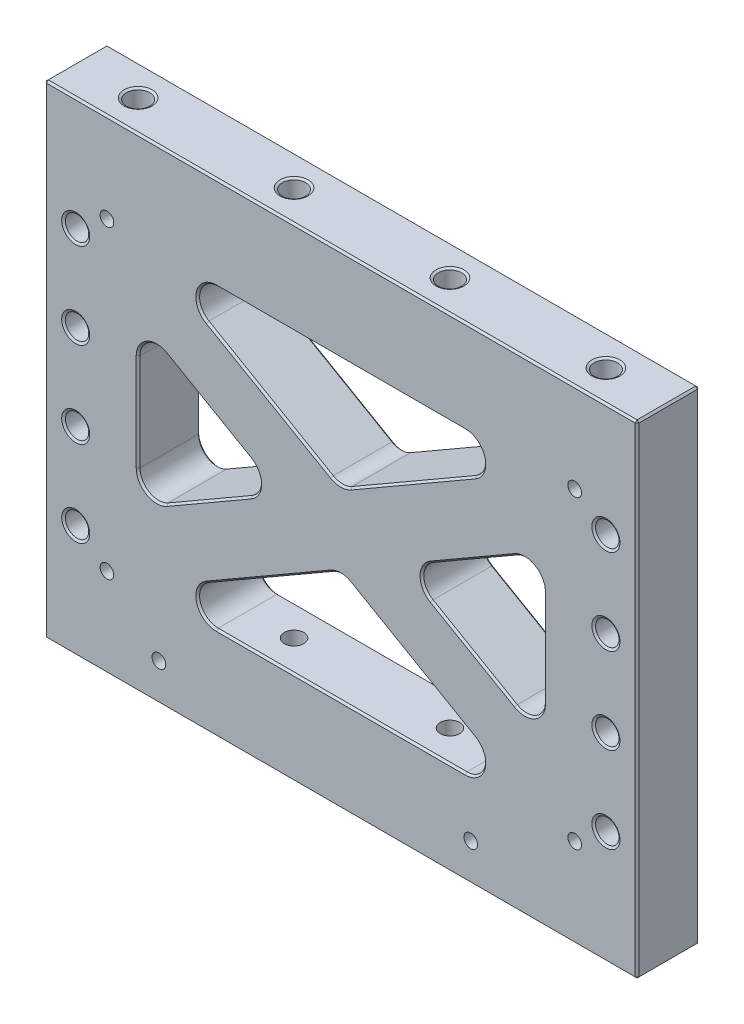
SolidWorks part; units mm, degrees
material "6061-T6 Al"
ref_plane "Front" through (0, 0, 0) normal (0, 0, 1) x (1, 0, 0)
ref_plane "Top" through (0, 0, 0) normal (0, 1, 0) x (1, 0, 0)
ref_plane "Right" through (0, 0, 0) normal (1, 0, 0) x (0, 0, -1)
sketch "Sketch1" plane through (0, 0, 0) normal (0, 0, 1) x (1, 0, 0)
  line L1 (-120.65, 0) -> (120.65, 0)
  line L2 (-120.65, 0) -> (-120.65, 196.85)
  line L3 (-120.65, 196.85) -> (120.65, 196.85)
  line L4 (120.65, 0) -> (120.65, 196.85)
  dimension "D1" = 241.3
  dimension "D2" = 196.85
extrude "Extrude1" add sketch "Sketch1" along normal blind 25.4
sketch "Sketch8" plane through (0, 0, 25.4) normal (0, 0, 1) x (1, 0, 0)
  line L0 (0, 158.75) -> (0, 196.85) construction
  line L1 (-82.55, 158.75) -> (82.55, 158.75)
  line L2 (-82.55, 158.75) -> (-82.55, 38.1)
  line L3 (-82.55, 38.1) -> (82.55, 38.1)
  line L4 (82.55, 158.75) -> (82.55, 38.1)
  line L5 (120.65, 196.85) -> (-120.65, 196.85) construction
  line L6 (0, 0) -> (0, 38.1) construction
  line L7 (-120.65, 0) -> (120.65, 0) construction
  line L8 (120.65, 0) -> (120.65, 196.85) construction
  point P4 (0, 38.1)
  dimension "D1" = 38.1
  dimension "D2" = 38.1
extrude "Extrude2" cut sketch "Sketch8" against normal through all
sketch "Sketch9" plane through (0, 0, 25.4) normal (0, 0, 1) x (1, 0, 0)
  line L0 (-82.55, 146.0853) -> (82.55, 50.7647) construction
  line L1 (-82.55, 38.1) -> (82.55, 38.1) construction
  line L2 (0, 98.425) -> (120.65, 98.425) construction
  line L3 (120.65, 0) -> (120.65, 196.85) construction
  line L4 (82.55, 38.1) -> (82.55, 158.75) construction
  line L5 (-82.55, 158.75) -> (-82.55, 131.4206)
  line L6 (-82.55, 158.75) -> (-82.55, 38.1) construction
  line L7 (-82.55, 131.4206) -> (79.086, 38.1)
  line L8 (79.086, 38.1) -> (82.55, 38.1)
  line L9 (82.55, 38.1) -> (82.55, 65.4294)
  line L10 (82.55, 65.4294) -> (-79.086, 158.75)
  line L11 (82.55, 158.75) -> (-82.55, 158.75) construction
  line L12 (-79.086, 158.75) -> (-82.55, 158.75)
  line L13 (-6.35, 87.4265) -> (0, 98.425) construction
  line L14 (0, 98.425) -> (6.35, 109.4235) construction
  dimension "D1" = 30
  dimension "D2" = 25.4
extrude "Extrude3" add sketch "Sketch9" against normal up to surface (25.4 mm away) up to face at (0, 98.425, 0)
mirror "Mirror1" about plane through (0, 0, 0) normal (1, 0, 0) of "Extrude3"
fillet "Fillet1" radius 7.62 12 edges at (79.086, 38.1, 12.7) (-79.086, 38.1, 12.7) (0, 83.7603, 12.7) (79.086, 158.75, 12.7) (0, 113.0897, 12.7) (-82.55, 65.4294, 12.7) (-82.55, 131.4206, 12.7) (-25.4, 98.425, 12.7) (82.55, 131.4206, 12.7) (82.55, 65.4294, 12.7) (25.4, 98.425, 12.7) (-79.086, 158.75, 12.7)
chamfer "Chamfer1" distance 0.762 angle 45 48 edges at (29.1339, 66.9399, 25.4) (29.1339, 66.9399, 0) (58.0081, 43.7478, 25.4) (0, 82.5815, 25.4) (0, 38.1, 25.4) (-29.1339, 66.9399, 25.4) (-29.1339, 66.9399, 0) (-58.0081, 43.7478, 25.4) (0, 82.5815, 0) (58.0081, 43.7478, 0) (0, 38.1, 0) (-58.0081, 43.7478, 0) (53.975, 114.9228, 0) (53.975, 114.9228, 25.4) (78.74, 124.8215, 25.4) (33.02, 98.425, 25.4) (82.55, 98.425, 25.4) (53.975, 81.9272, 25.4) (53.975, 81.9272, 0) (78.74, 72.0285, 25.4) (33.02, 98.425, 0) (78.74, 124.8215, 0) (82.55, 98.425, 0) (78.74, 72.0285, 0) (0, 158.75, 0) (-58.0081, 153.1022, 0) (58.0081, 153.1022, 0) (-29.1339, 129.9101, 25.4) (-29.1339, 129.9101, 0) (29.1339, 129.9101, 25.4) (29.1339, 129.9101, 0) (0, 114.2685, 0) (0, 158.75, 25.4) (58.0081, 153.1022, 25.4) (-58.0081, 153.1022, 25.4) (0, 114.2685, 25.4) (-53.975, 114.9228, 25.4) (-53.975, 114.9228, 0) (-33.02, 98.425, 25.4) (-78.74, 124.8215, 25.4) (-53.975, 81.9272, 0) (-53.975, 81.9272, 25.4) (-82.55, 98.425, 25.4) (-78.74, 72.0285, 25.4) (-78.74, 124.8215, 0) (-33.02, 98.425, 0) (-82.55, 98.425, 0) (-78.74, 72.0285, 0)
chamfer "Chamfer2" distance 0.762 angle 45 12 edges at (-120.65, 98.425, 25.4) (-120.65, 98.425, 0) (-120.65, 0, 12.7) (0, 0, 25.4) (0, 0, 0) (120.65, 0, 12.7) (120.65, 98.425, 25.4) (120.65, 98.425, 0) (120.65, 196.85, 12.7) (0, 196.85, 25.4) (-120.65, 196.85, 12.7) (0, 196.85, 0)
hole_wizard "3/8-16 Tapped Hole1" positions "Sketch5" profile "Sketch4" tap size "3/8-16" standard "Ansi Inch"
sketch "Sketch5" plane through (0, 196.85, 0) normal (0, 1, 0) x (-1, 0, 0)
  line L2 (-95.25, 12.7) -> (-31.75, 12.7) construction
  line L3 (-31.75, 12.7) -> (31.75, 12.7) construction
  line L4 (31.75, 12.7) -> (95.25, 12.7) construction
  line L7 (120.65, 25.4) -> (120.65, 0) construction
  point P1 (31.75, 12.7)
  point P3 (-31.75, 12.7)
  point P42 (0, 12.7)
  point P46 (120.65, 12.7)
  dimension "D1" = 63.5
sketch "Sketch4" plane through (-31.75, 196.85, 12.7) normal (1, 0, 0) x (0, 0, 1)
  line L0 (0, 0) -> (0, 40.4847)
  line L1 (0, 40.4847) -> (3.9687, 38.1)
  line L2 (3.9687, 38.1) -> (3.9687, 25.4)
  line L3 (3.9687, 25.4) -> (4.7625, 25.4)
  line L5 (4.7625, 25.4) -> (4.7625, 0.5499)
  line L6 (4.7625, 0.5499) -> (5.715, 0)
  line L7 (5.715, 0) -> (0, 0)
  line L8 (-4.7625, 0.5499) -> (-5.715, 0) construction
  line L10 (0, 40.4847) -> (-3.9688, 38.1) construction
  line L11 (0, -6.35) -> (0, 107.95) construction
  dimension "Tap Drill Dia." = 7.9375
  dimension "Tap Drill Depth" = 38.1
  dimension "Thread Major Dia." = 9.525
  dimension "Thread Depth" = 25.4
  dimension "Near C'Sink Dia." = 11.43
  dimension "Near C'Sink Angle" = 120
  dimension "Drill Angle" = 118
hole_wizard "3/8-16 Tapped Hole2" positions "Sketch29" profile "Sketch28" tap size "3/8-16" standard "Ansi Inch"
sketch "Sketch29" plane through (0, 0, 0) normal (0, -1, 0) x (1, 0, 0)
  point P1 (-31.75, 12.7)
  point P4 (31.75, 12.7)
sketch "Sketch28" plane through (-31.75, 0, 12.7) normal (1, 0, 0) x (0, 0, -1)
  line L0 (0, 0) -> (0, 40.4847)
  line L1 (0, 40.4847) -> (3.9687, 38.1)
  line L2 (3.9687, 38.1) -> (3.9687, 25.4)
  line L3 (3.9687, 25.4) -> (4.7625, 25.4)
  line L5 (4.7625, 25.4) -> (4.7625, 0.5499)
  line L6 (4.7625, 0.5499) -> (5.715, 0)
  line L7 (5.715, 0) -> (0, 0)
  line L8 (-4.7625, 0.5499) -> (-5.715, 0) construction
  line L10 (0, 40.4847) -> (-3.9688, 38.1) construction
  line L11 (0, -6.35) -> (0, 107.95) construction
  dimension "Tap Drill Dia." = 7.9375
  dimension "Tap Drill Depth" = 38.1
  dimension "Thread Major Dia." = 9.525
  dimension "Thread Depth" = 25.4
  dimension "Near C'Sink Dia." = 11.43
  dimension "Near C'Sink Angle" = 120
  dimension "Drill Angle" = 118
hole_wizard "3/8-16 Tapped Hole3" positions "Sketch35" profile "Sketch34" tap size "3/8-16" standard "Ansi Inch"
sketch "Sketch35" plane through (0, 196.85, 0) normal (0, 1, 0) x (-1, 0, 0)
  line L0 (-95.25, 12.7) -> (-31.75, 12.7) construction
  line L3 (31.75, 12.7) -> (95.25, 12.7) construction
  line L6 (-31.75, 12.7) -> (31.75, 12.7) construction
  point P0 (95.25, 12.7)
  point P1 (-95.25, 12.7)
sketch "Sketch34" plane through (-95.25, 196.85, 12.7) normal (1, 0, 0) x (0, 0, 1)
  line L0 (0, 0) -> (0, 40.4847)
  line L1 (0, 40.4847) -> (3.9687, 38.1)
  line L2 (3.9687, 38.1) -> (3.9687, 25.4)
  line L3 (3.9687, 25.4) -> (4.7625, 25.4)
  line L5 (4.7625, 25.4) -> (4.7625, 0.5499)
  line L6 (4.7625, 0.5499) -> (5.715, 0)
  line L7 (5.715, 0) -> (0, 0)
  line L8 (-4.7625, 0.5499) -> (-5.715, 0) construction
  line L10 (0, 40.4847) -> (-3.9688, 38.1) construction
  line L11 (0, -6.35) -> (0, 107.95) construction
  dimension "Tap Drill Dia." = 7.9375
  dimension "Tap Drill Depth" = 38.1
  dimension "Thread Major Dia." = 9.525
  dimension "Thread Depth" = 25.4
  dimension "Near C'Sink Dia." = 11.43
  dimension "Near C'Sink Angle" = 120
  dimension "Drill Angle" = 118
hole_wizard "3/8-16 Tapped Hole4" positions "Sketch37" profile "Sketch36" tap size "3/8-16" standard "Ansi Inch"
sketch "Sketch37" plane through (0, 0, 0) normal (0, -1, 0) x (1, 0, 0)
  point P0 (95.25, 12.7)
  point P4 (-95.25, 12.7)
sketch "Sketch36" plane through (95.25, 0, 12.7) normal (1, 0, 0) x (0, 0, -1)
  line L0 (0, 0) -> (0, 40.4847)
  line L1 (0, 40.4847) -> (3.9687, 38.1)
  line L2 (3.9687, 38.1) -> (3.9687, 25.4)
  line L3 (3.9687, 25.4) -> (4.7625, 25.4)
  line L5 (4.7625, 25.4) -> (4.7625, 0.5499)
  line L6 (4.7625, 0.5499) -> (5.715, 0)
  line L7 (5.715, 0) -> (0, 0)
  line L8 (-4.7625, 0.5499) -> (-5.715, 0) construction
  line L10 (0, 40.4847) -> (-3.9688, 38.1) construction
  line L11 (0, -6.35) -> (0, 107.95) construction
  dimension "Tap Drill Dia." = 7.9375
  dimension "Tap Drill Depth" = 38.1
  dimension "Thread Major Dia." = 9.525
  dimension "Thread Depth" = 25.4
  dimension "Near C'Sink Dia." = 11.43
  dimension "Near C'Sink Angle" = 120
  dimension "Drill Angle" = 118
hole_wizard "7/32 (0.21875) Vent Hole1" positions "Sketch3" profile "Sketch2" hole size "7/32" standard "Ansi Inch" end condition through all
sketch "Sketch3" plane through (0, 0, 25.4) normal (0, 0, 1) x (1, 0, 0)
  line L15 (31.75, 160.528) -> (95.25, 160.528) construction
  line L16 (-31.75, 160.528) -> (31.75, 160.528) construction
  line L17 (-95.25, 160.528) -> (-31.75, 160.528) construction
  line L26 (0, 160.528) -> (0, 196.85) construction
  line L27 (120.65, 196.85) -> (-120.65, 196.85) construction
  line L29 (-95.25, 36.322) -> (-95.25, 0) construction
  line L30 (119.888, 0) -> (-119.888, 0) construction
  line L32 (-119.888, 196.85) -> (119.888, 196.85) construction
  point P69 (-95.25, 160.528)
  point P75 (95.25, 160.528)
  point P95 (-95.25, 36.322)
  point P101 (95.25, 36.322)
  dimension "D1" = 36.322
  dimension "D2" = 63.5
sketch "Sketch2" plane through (-95.25, 160.528, 25.4) normal (1, 0, 0) x (0, -1, 0)
  line L0 (0, 0) -> (0, 25.4)
  line L1 (0, 25.4) -> (2.7781, 25.4)
  line L2 (2.7781, 25.4) -> (2.7781, 0)
  line L5 (2.7781, 0) -> (0, 0)
  line L11 (0, -6.35) -> (0, 107.95) construction
  dimension "Thru Hole Dia." = 5.5562
  dimension "Thru Hole Depth" = 25.4
hole_wizard "3/8-16 Tapped Hole5" positions "Sketch33" profile "Sketch32" tap size "3/8-16" standard "Ansi Inch" end condition through all
sketch "Sketch33" plane through (32.6062, 166.8277, 0) normal (0, 0, -1) x (-1, 0, 0)
  line L0 (-75.3438, -16.0152) -> (-75.3438, -50.9402) construction
  line L1 (-75.3438, -50.9402) -> (-75.3438, -85.8652) construction
  line L2 (-75.3438, -85.8652) -> (-75.3438, -120.7902) construction
  line L9 (140.5562, -16.0152) -> (153.2562, -16.0152) construction
  line L10 (153.2562, 29.2603) -> (153.2562, -166.0657) construction
  line L13 (-75.3438, -68.4027) -> (-88.0438, -68.4027) construction
  line L14 (-88.0438, -166.0657) -> (-88.0438, 29.2603) construction
  point P0 (-75.3438, -16.0152)
  point P3 (-75.3438, -50.9402)
  point P5 (-75.3438, -85.8652)
  point P7 (-75.3438, -120.7902)
  point P9 (140.5562, -120.7902)
  point P11 (140.5562, -85.8652)
  point P13 (140.5562, -50.9402)
  point P15 (140.5562, -16.0152)
  dimension "D1" = 34.925
  dimension "D2" = 12.7
sketch "Sketch32" plane through (107.95, 150.8125, 0) normal (1, 0, 0) x (0, 1, 0)
  line L0 (0, 0) -> (0, 25.4)
  line L1 (0, 25.4) -> (5.715, 25.4)
  line L2 (4.7625, 24.8501) -> (4.7625, 0.5499)
  line L3 (4.7625, 0.5499) -> (5.715, 0)
  line L5 (5.715, 0) -> (0, 0)
  line L6 (-4.7625, 0.5499) -> (-5.715, 0) construction
  line L7 (5.715, 25.4) -> (4.7625, 24.8501)
  line L8 (-5.715, 25.4) -> (-4.7625, 24.8501) construction
  line L11 (0, -6.35) -> (0, 107.95) construction
  dimension "Thread Major Dia." = 9.525
  dimension "Thru Tap Drill Depth" = 25.4
  dimension "Near C'Sink Dia." = 11.43
  dimension "Near C'Sink Angle" = 120
  dimension "Far C'Sink Dia." = 11.43
  dimension "Far C'Sink Angle" = 120
sketch "Sketch38" [suppressed] plane through (0, 0, 0) normal (0, -1, 0) x (1, 0, 0)
  line L4 (-120.65, 0) -> (120.65, 0)
  line L5 (120.65, 0) -> (120.65, 25.4)
  line L6 (120.65, 25.4) -> (-120.65, 25.4)
  line L7 (-120.65, 25.4) -> (-120.65, 0)
  line L8 (-120.65, 0) -> (120.65, 0)
  line L9 (120.65, 0) -> (120.65, 25.4)
  line L10 (120.65, 25.4) -> (-120.65, 25.4)
  line L11 (-120.65, 25.4) -> (-120.65, 0)
  dimension "D1" = 0
extrude "Extrude4" [suppressed] cut sketch "Sketch38" against normal blind 0.0254
sketch "Sketch39" [suppressed] plane through (0, 196.85, 0) normal (0, 1, 0) x (1, 0, 0)
  line L4 (120.65, 0) -> (-120.65, 0)
  line L5 (-120.65, 0) -> (-120.65, -25.4)
  line L6 (-120.65, -25.4) -> (120.65, -25.4)
  line L7 (120.65, -25.4) -> (120.65, 0)
  line L8 (120.65, 0) -> (-120.65, 0)
  line L9 (-120.65, 0) -> (-120.65, -25.4)
  line L10 (-120.65, -25.4) -> (120.65, -25.4)
  line L11 (120.65, -25.4) -> (120.65, 0)
  dimension "D1" = 0
extrude "Extrude5" [suppressed] cut sketch "Sketch39" against normal blind 0.0254
sketch "Sketch40" [suppressed] plane through (0, 0.0254, 0) normal (0, -1, 0) x (1, 0, 0)
  line L0 (120.65, 25.4) -> (-120.65, 25.4) construction
  line L1 (-44.45, 25.4) -> (-19.05, 25.4)
  line L2 (-44.45, 25.4) -> (-44.45, 0)
  line L3 (-44.45, 0) -> (-19.05, 0)
  line L4 (-19.05, 25.4) -> (-19.05, 0)
  line L5 (-120.65, 0) -> (120.65, 0) construction
  line L6 (-82.55, 12.7) -> (-44.45, 12.7) construction
  line L7 (-107.95, 25.4) -> (-82.55, 25.4)
  line L8 (-107.95, 25.4) -> (-107.95, 0)
  line L9 (-107.95, 0) -> (-82.55, 0)
  line L10 (-82.55, 25.4) -> (-82.55, 0)
  line L11 (19.05, 25.4) -> (44.45, 25.4)
  line L12 (19.05, 25.4) -> (19.05, 0)
  line L13 (19.05, 0) -> (44.45, 0)
  line L14 (44.45, 25.4) -> (44.45, 0)
  line L15 (82.55, 25.4) -> (107.95, 25.4)
  line L16 (82.55, 25.4) -> (82.55, 0)
  line L17 (82.55, 0) -> (107.95, 0)
  line L18 (107.95, 25.4) -> (107.95, 0)
  line L19 (-19.05, 12.7) -> (19.05, 12.7) construction
  line L20 (44.45, 12.7) -> (82.55, 12.7) construction
  point P27 (0, 12.7)
  dimension "D1" = 38.1
  dimension "D2" = 25.4
extrude "Extrude6" [suppressed] add sketch "Sketch40" along normal blind 0.0254
sketch "Sketch41" [suppressed] plane through (0, 196.8246, 0) normal (0, 1, 0) x (1, 0, 0)
  line L0 (120.65, 0) -> (-120.65, 0) construction
  line L1 (-107.95, 0) -> (-82.55, 0)
  line L2 (-107.95, 0) -> (-107.95, -25.4)
  line L3 (-107.95, -25.4) -> (-82.55, -25.4)
  line L4 (-82.55, 0) -> (-82.55, -25.4)
  line L5 (-120.65, -25.4) -> (120.65, -25.4) construction
  line L6 (-82.55, -12.7) -> (-44.45, -12.7) construction
  line L7 (-44.45, 0) -> (-19.05, 0)
  line L8 (-44.45, 0) -> (-44.45, -25.4)
  line L9 (-44.45, -25.4) -> (-19.05, -25.4)
  line L10 (-19.05, 0) -> (-19.05, -25.4)
  line L11 (19.05, 0) -> (44.45, 0)
  line L12 (19.05, 0) -> (19.05, -25.4)
  line L13 (19.05, -25.4) -> (44.45, -25.4)
  line L14 (44.45, 0) -> (44.45, -25.4)
  line L15 (82.55, 0) -> (107.95, 0)
  line L16 (82.55, 0) -> (82.55, -25.4)
  line L17 (82.55, -25.4) -> (107.95, -25.4)
  line L18 (107.95, 0) -> (107.95, -25.4)
  line L19 (-19.05, -12.7) -> (19.05, -12.7) construction
  line L20 (44.45, -12.7) -> (82.55, -12.7) construction
  point P26 (0, -12.7)
  dimension "D1" = 38.1
  dimension "D2" = 25.4
extrude "Extrude7" [suppressed] add sketch "Sketch41" along normal blind 0.0254
sketch "Sketch42" [suppressed] plane through (0, 196.85, 0) normal (0, 1, 0) x (1, 0, 0)
  line L0 (107.95, -25.4) -> (107.95, 0) construction
  line L1 (-107.95, 0) -> (107.95, 0)
  line L2 (-107.95, 0) -> (-107.95, -3.81)
  line L3 (-107.95, -3.81) -> (107.95, -3.81)
  line L4 (107.95, 0) -> (107.95, -3.81)
  line L5 (-107.95, 0) -> (-107.95, -25.4) construction
  line L6 (107.95, -25.4) -> (-107.95, -25.4)
  line L7 (107.95, -25.4) -> (107.95, -21.59)
  line L8 (107.95, -21.59) -> (-107.95, -21.59)
  line L9 (-107.95, -25.4) -> (-107.95, -21.59)
  dimension "D1" = 3.81
extrude "Extrude8" [suppressed] cut sketch "Sketch42" against normal up to surface (0.0254 mm away)
sketch "Sketch43" [suppressed] plane through (0, 0, 0) normal (0, -1, 0) x (1, 0, 0)
  line L0 (107.95, 0) -> (107.95, 25.4) construction
  line L1 (-107.95, 25.4) -> (107.95, 25.4)
  line L2 (-107.95, 25.4) -> (-107.95, 21.59)
  line L3 (-107.95, 21.59) -> (107.95, 21.59)
  line L4 (107.95, 25.4) -> (107.95, 21.59)
  line L5 (-107.95, 25.4) -> (-107.95, 0) construction
  line L6 (107.95, 0) -> (-107.95, 0)
  line L7 (107.95, 0) -> (107.95, 3.81)
  line L8 (107.95, 3.81) -> (-107.95, 3.81)
  line L9 (-107.95, 0) -> (-107.95, 3.81)
  dimension "D1" = 3.81
extrude "Extrude9" [suppressed] cut sketch "Sketch43" against normal up to surface (0.0254 mm away)
sketch "Sketch44" [suppressed] plane through (0, 0, 25.4) normal (0, 0, 1) x (1, 0, 0)
  line L0 (-82.55, 131.4206) -> (-82.55, 65.4294)
  line L1 (-82.55, 65.4294) -> (-25.4, 98.425)
  line L2 (-25.4, 98.425) -> (-82.55, 131.4206)
  line L3 (-71.12, 124.8215) -> (-36.83, 105.0241) construction
  line L4 (-71.12, 72.0285) -> (-36.83, 91.8259) construction
  line L5 (-82.55, 118.2223) -> (-82.55, 78.6277) construction
  line L6 (0, 0) -> (0, 144.8149) construction
  line L7 (33.02, 98.425) -> (98.86, 98.425) construction
  line L8 (25.4, 98.425) -> (82.55, 131.4206)
  line L9 (82.55, 65.4294) -> (25.4, 98.425)
  line L10 (82.55, 131.4206) -> (82.55, 65.4294)
  line L11 (-79.086, 158.75) -> (0, 113.0897)
  line L12 (0, 113.0897) -> (79.086, 158.75)
  line L13 (79.086, 158.75) -> (-79.086, 158.75)
  line L14 (50.6477, 158.75) -> (-50.6477, 158.75) construction
  line L15 (-3.81, 115.2894) -> (-54.4577, 144.5309) construction
  line L16 (3.81, 115.2894) -> (54.4577, 144.5309) construction
  line L17 (0, 83.7603) -> (79.086, 38.1)
  line L18 (79.086, 38.1) -> (-79.086, 38.1)
  line L19 (-79.086, 38.1) -> (0, 83.7603)
  arc A0 (36.83, 105.0241) -> (36.83, 91.8259) centre (40.64, 98.425) ccw construction
extrude "Extrude10" [suppressed] cut sketch "Sketch44" against normal through all
hole_wizard "3/8 (0.375) Diameter Hole1" positions "Sketch46" profile "Sketch45" hole size "3/8" standard "Ansi Inch"
sketch "Sketch46" plane through (0, 0, 0) normal (0, -1, 0) x (1, 0, 0)
  line L0 (-95.25, 12.7) -> (-74.0833, 12.7) construction
  line L1 (-74.0833, 12.7) -> (-52.9167, 12.7) construction
  line L2 (-52.9167, 12.7) -> (-31.75, 12.7) construction
  point P0 (-74.0833, 12.7)
sketch "Sketch45" plane through (-74.0833, 0, 12.7) normal (1, 0, 0) x (0, 0, -1)
  line L0 (0, 0) -> (0, 21.9169)
  line L1 (0, 21.9169) -> (4.7714, 19.05)
  line L2 (4.7714, 19.05) -> (4.7714, 2.3406)
  line L3 (4.7714, 2.3406) -> (7.112, 0)
  line L5 (7.112, 0) -> (0, 0)
  line L6 (-4.7714, 2.3406) -> (-7.112, 0) construction
  line L10 (0, 21.9169) -> (-4.7714, 19.05) construction
  line L11 (0, -6.35) -> (0, 107.95) construction
  dimension "Hole Dia." = 9.5428
  dimension "Hole Depth" = 19.05
  dimension "Near C'Sink Dia." = 14.224
  dimension "Near C'Sink Angle" = 90
  dimension "Drill Angle" = 118
sketch "Sketch47" plane through (0, 0, 0) normal (0, -1, 0) x (1, 0, 0)
  line L0 (51.3292, 12.7) -> (54.5042, 12.7) construction
  line L1 (51.3292, 17.4714) -> (54.5042, 17.4714)
  line L2 (51.3292, 7.9286) -> (54.5042, 7.9286)
  line L3 (31.75, 12.7) -> (52.9167, 12.7) construction
  line L4 (-95.25, 12.7) -> (-74.0833, 12.7) construction
  arc A0 (51.3292, 17.4714) -> (51.3292, 7.9286) centre (51.3292, 12.7) ccw
  arc A1 (54.5042, 7.9286) -> (54.5042, 17.4714) centre (54.5042, 12.7) ccw
  point P2 (52.9167, 12.7)
  dimension "D1" = 3.175
  dimension "D2" = 9.5428
extrude "Extrude11" cut sketch "Sketch47" against normal blind 19.05
chamfer "Chamfer3" distance 2.286 angle 45 4 edges at (59.2756, 0, 12.7) (52.9167, 0, 17.4714) (52.9167, 0, 7.9286) (46.5578, 0, 12.7)
hole_wizard "7/32 (0.21875) Diameter Hole2" positions "Sketch49" profile "Sketch48" hole size "7/32" standard "Ansi Inch" end condition through all
sketch "Sketch49" plane through (0, 0, 25.4) normal (0, 0, 1) x (1, 0, 0)
  line L0 (119.888, 0) -> (-119.888, 0) construction
  point P0 (-74.0833, 15.24)
  point P1 (52.9167, 15.24)
  dimension "D1" = 15.24
sketch "Sketch48" plane through (-74.0833, 15.24, 25.4) normal (1, 0, 0) x (0, -1, 0)
  line L0 (0, 0) -> (0, 25.4)
  line L1 (0, 25.4) -> (2.7781, 25.4)
  line L2 (2.7781, 25.4) -> (2.7781, 0)
  line L5 (2.7781, 0) -> (0, 0)
  line L11 (0, -6.35) -> (0, 107.95) construction
  dimension "Thru Hole Dia." = 5.5562
  dimension "Thru Hole Depth" = 25.4
